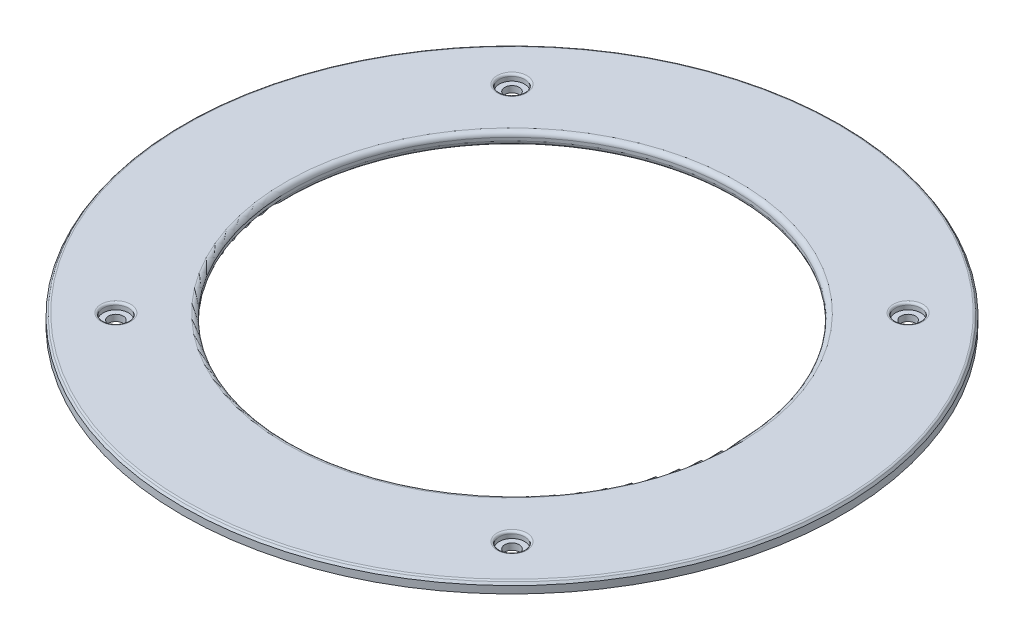
SolidWorks part; units mm, degrees
ref_plane "Front Plane" through (0, 0, 0) normal (0, 0, 1) x (1, 0, 0)
ref_plane "Top Plane" through (0, 0, 0) normal (0, 1, 0) x (1, 0, 0)
ref_plane "Right Plane" through (0, 0, 0) normal (1, 0, 0) x (0, 0, -1)
sketch "Sketch2" plane through (0, 0, 0) normal (0, 1, 0) x (1, 0, 0)
  circle A0 centre (0, 0) radius 104
  dimension "D1" = 208
extrude "Boss-Extrude3" add sketch "Sketch2" along normal blind 4
sketch "Sketch3" plane through (0, 4, 0) normal (0, 1, 0) x (1, 0, 0)
  line L1 (-62.5, -62.5) -> (62.5, -62.5)
  line L2 (-62.5, -62.5) -> (-62.5, 62.5)
  line L3 (-62.5, 62.5) -> (62.5, 62.5)
  line L4 (62.5, -62.5) -> (62.5, 62.5)
  line L5 (-62.5, -62.5) -> (62.5, 62.5) construction
  line L6 (-62.5, 62.5) -> (62.5, -62.5) construction
  point P0 (0, 0)
  dimension "D1" = 125
  dimension "D2" = 125
sketch "Sketch6" plane through (0, 4, 0) normal (0, 1, 0) x (1, 0, 0)
  point P0 (-62.5, 62.5)
  point P3 (62.5, 62.5)
  point P6 (62.5, -62.5)
  point P9 (-62.5, -62.5)
hole_wizard "CBORE for M5 Hex Head Bolt1" positions "Sketch6" profile "Sketch5" counterbore size "M5" standard "ISO" end condition through all
sketch "Sketch5" plane through (-62.5, 4, -62.5) normal (1, 0, 0) x (0, 0, 1)
  line L0 (0, 0) -> (0, 4)
  line L1 (0, 4) -> (2.3, 4)
  line L3 (2.3, 4) -> (2.3, 2)
  line L4 (2.3, 2) -> (4, 2)
  line L5 (4, 2) -> (4, 0)
  line L7 (4, 0) -> (0, 0)
  line L11 (0, -6.35) -> (0, 107.95) construction
  dimension "Thru Hole Dia." = 4.6
  dimension "Thru Hole Depth" = 4
  dimension "C'Bore Dia." = 8
  dimension "C'Bore Depth" = 2
sketch "Sketch7" plane through (0, 4, 0) normal (0, 1, 0) x (1, 0, 0)
  line L0 (-62.5, -62.5) -> (62.5, 62.5) construction
  line L1 (-70, -70) -> (70, -70)
  line L2 (-70, -70) -> (-70, 70)
  line L3 (-70, 70) -> (70, 70)
  line L4 (70, -70) -> (70, 70)
  line L5 (-70, -70) -> (70, 70) construction
  line L6 (-70, 70) -> (70, -70) construction
  circle A0 centre (0, 0) radius 70
  point P1 (0, 0)
  dimension "D1" = 140
extrude "Cut-Extrude1" cut sketch "Sketch7" against normal blind 4 contours A0
fillet "Fillet1" radius 1.5 2 edges at (0, 4, 70) (0, 0, 70)
chamfer "Chamfer1" distance 1 angle 35 2 edges at (0, 0, 104) (0, 4, 104)
fillet "Fillet2" radius 0.7 4 edges at (-62.5, 4, 66.5) (-62.5, 4, -58.5) (62.5, 4, -58.5) (62.5, 4, 66.5)
fillet "Fillet3" radius 0.7 1 edges at (0, 0, 103)
fillet "Fillet4" radius 0.7 1 edges at (0, 4, 103.2998)
